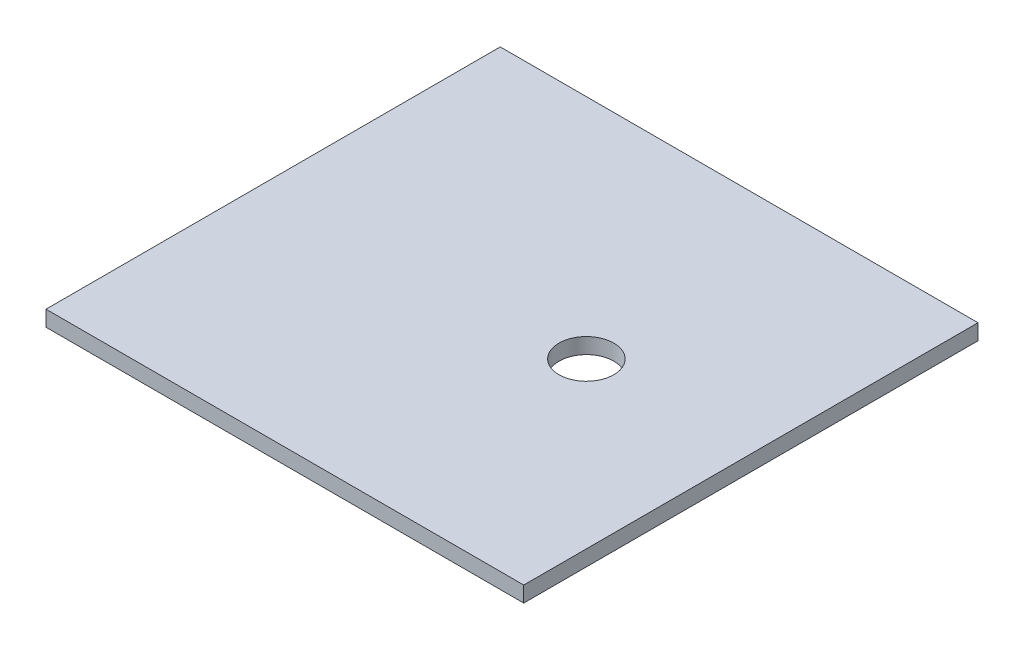
SolidWorks part; units mm, degrees
material "Acrylic (Medium-high impact)"
ref_plane "Front Plane" through (0, 0, 0) normal (0, 0, 1) x (1, 0, 0)
ref_plane "Top Plane" through (0, 0, 0) normal (0, 1, 0) x (1, 0, 0)
ref_plane "Right Plane" through (0, 0, 0) normal (1, 0, 0) x (0, 0, -1)
sketch "Sketch1" plane through (0, 0, 0) normal (0, 1, 0) x (1, 0, 0)
  line L0 (25, 0) -> (101.8483, 76.8483) construction
  line L1 (-175, 145) -> (130, 145)
  line L2 (-175, 145) -> (-175, -145)
  line L3 (-175, -145) -> (130, -145)
  line L5 (-165, 135) -> (130, 135) construction
  line L6 (-165, 135) -> (-165, -135) construction
  line L7 (-165, -135) -> (130, -135) construction
  line L9 (25, 0) -> (25, 93.5438) construction
  line L10 (130, 145) -> (130, -145)
  circle A0 centre (25, 0) radius 17.5
  circle A1 centre (25, 0) radius 45 construction
  circle A2 centre (25, 0) radius 70 construction
  point P28 (25, 0)
  point P35 (25, 0)
  point P51 (25, 0)
  dimension "D10" = 35
  dimension "D12" = 140
  dimension "D13" = 90
  dimension "D1" = 290
  dimension "D3" = 175
  dimension "D4" = 145
  dimension "D5" = 10
  dimension "D6" = 10
  dimension "D8" = 10
  dimension "D11" = 145
  dimension "D15" = 45
extrude "Boss-Extrude1" add sketch "Sketch1" along normal blind 10
